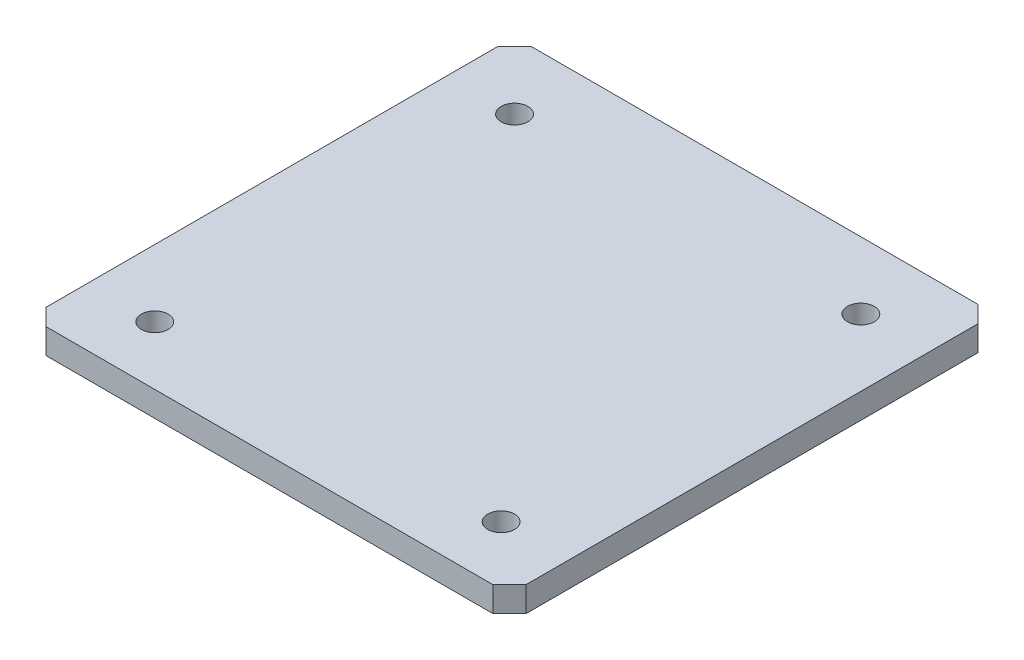
SolidWorks part; units mm, degrees
material "PLA"
ref_plane "Front Plane" through (0, 0, 0) normal (0, 0, 1) x (1, 0, 0)
ref_plane "Top Plane" through (0, 0, 0) normal (0, 1, 0) x (1, 0, 0)
ref_plane "Right Plane" through (0, 0, 0) normal (1, 0, 0) x (0, 0, -1)
sketch "Sketch1" plane through (0, 0, 0) normal (0, 1, 0) x (1, 0, 0)
  line L1 (0, 0) -> (287, 0)
  line L2 (0, 0) -> (0, 290)
  line L3 (0, 290) -> (287, 290)
  line L4 (287, 0) -> (287, 290)
  dimension "D1" = 290
  dimension "D2" = 287
extrude "Boss-Extrude1" add sketch "Sketch1" along normal mid plane 15
chamfer "Chamfer1" distance 10 angle 45 4 edges at (0, 0, -290) (287, 0, -290) (0, 0, 0) (287, 0, 0)
sketch "Sketch3" plane through (0, 7.5, 0) normal (0, 1, 0) x (1, 0, 0)
  circle A0 centre (40, 35) radius 8
  circle A1 centre (40, 250) radius 8
  circle A2 centre (247, 250) radius 8
  circle A3 centre (247, 35) radius 8
extrude "Cut-Extrude1" cut sketch "Sketch3" against normal blind 16
